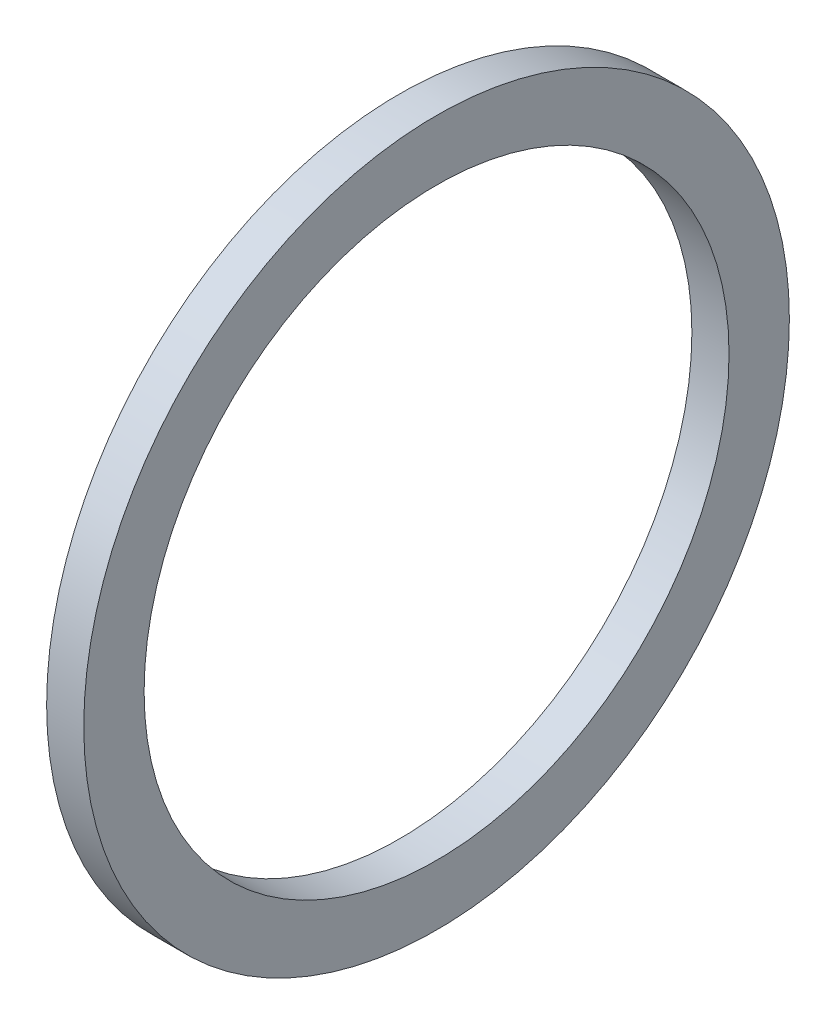
SolidWorks part; units mm, degrees
ref_plane "Front Plane" through (0, 0, 0) normal (0, 0, 1) x (1, 0, 0)
ref_plane "Top Plane" through (0, 0, 0) normal (0, 1, 0) x (1, 0, 0)
ref_plane "Right Plane" through (0, 0, 0) normal (1, 0, 0) x (0, 0, -1)
sketch "Sketch1" plane through (0, 0, 0) normal (0, 0, 1) x (1, 0, 0)
  line L0 (-43.7166, 0) -> (79.6876, 0) construction
  line L2 (0, -16.002) -> (2.032, -16.002)
  line L3 (0, -16.002) -> (0, -19.304)
  line L4 (0, -19.304) -> (2.032, -19.304)
  line L5 (2.032, -16.002) -> (2.032, -19.304)
  dimension "A" = 32.004
  dimension "B" = 38.608
  dimension "C" = 2.032
revolve "Revolve1" add sketch "Sketch1" angle 360 about L0
sketch "Sketch2" [suppressed] plane through (0, 0, 0) normal (0, 0, 1) x (1, 0, 0)
  line L0 (-34.685, 0) -> (47.6686, 0) construction
  circle A0 centre (2.54, -5.715) radius 0.762
  dimension "D1" = 2.54
  dimension "E" = 2.032
  dimension "D" = 28.956
revolve "Revolve3" [suppressed] add sketch "Sketch2" angle 360 about L0
